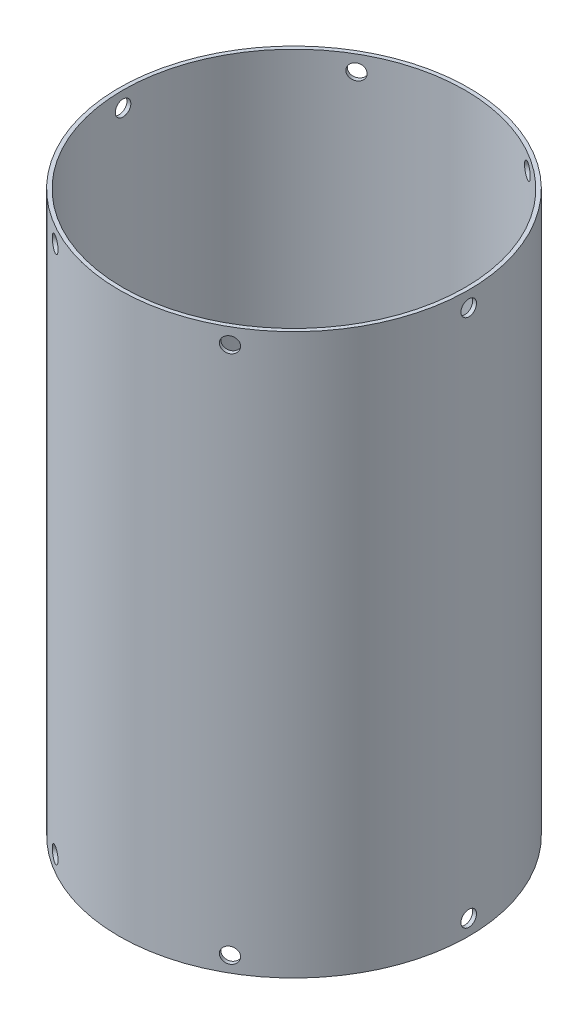
SolidWorks part; units mm, degrees
material "Hexcel AS4C (3000 Filaments)"
ref_plane "Front Plane" through (0, 0, 0) normal (0, 0, 1) x (1, 0, 0)
ref_plane "Top Plane" through (0, 0, 0) normal (0, 1, 0) x (1, 0, 0)
ref_plane "Right Plane" through (0, 0, 0) normal (1, 0, 0) x (0, 0, -1)
sketch "Sketch1" plane through (0, 0, 0) normal (0, 1, 0) x (1, 0, 0)
  circle A0 centre (0, 0) radius 142.875
  circle A1 centre (0, 0) radius 139.7
  dimension "D1" = 279.4
  dimension "D2" = 285.75
extrude "Boss-Extrude1" add sketch "Sketch1" along normal blind 457.2
ref_plane "Plane1" through (142.875, 0, 0) normal (1, 0, 0) x (0, 0, -1)
hole_wizard "1/2 (0.5) Diameter Hole1" positions "Sketch2" profile "Sketch3" hole size "1/2" standard "ANSI Inch"
sketch "Sketch2" plane through (142.875, 0, 0) normal (1, 0, 0) x (0, 0, -1)
  line L0 (0, 157.1625) -> (0, -157.1625) construction
  line L1 (142.875, 457.2) -> (-142.875, 457.2) construction
  point P0 (0, 444.5)
  dimension "D1" = 12.7
sketch "Sketch3" plane through (142.875, 444.5, 0) normal (0, 1, 0) x (0, 0, -1)
  line L0 (0, 0) -> (0, 333.7101)
  line L1 (0, 333.7101) -> (6.35, 333.7101)
  line L2 (6.35, 333.7101) -> (6.35, 0)
  line L5 (6.35, 0) -> (0, 0)
  line L11 (0, -6.35) -> (0, 107.95) construction
  dimension "Thru Hole Dia." = 12.7
  dimension "Thru Hole Depth" = 333.7101
pattern_circular "CirPattern1" count 6 over 360 about axis through (0, 457.2, 0) along (0, 1, 0) of "1/2 (0.5) Diameter Hole1"
ref_plane "Plane2" through (0, 228.6, 0) normal (0, 1, 0) x (1, 0, 0)
mirror "Mirror1" about plane through (0, 228.6, 0) normal (0, 1, 0) of "CirPattern1", "1/2 (0.5) Diameter Hole1"
